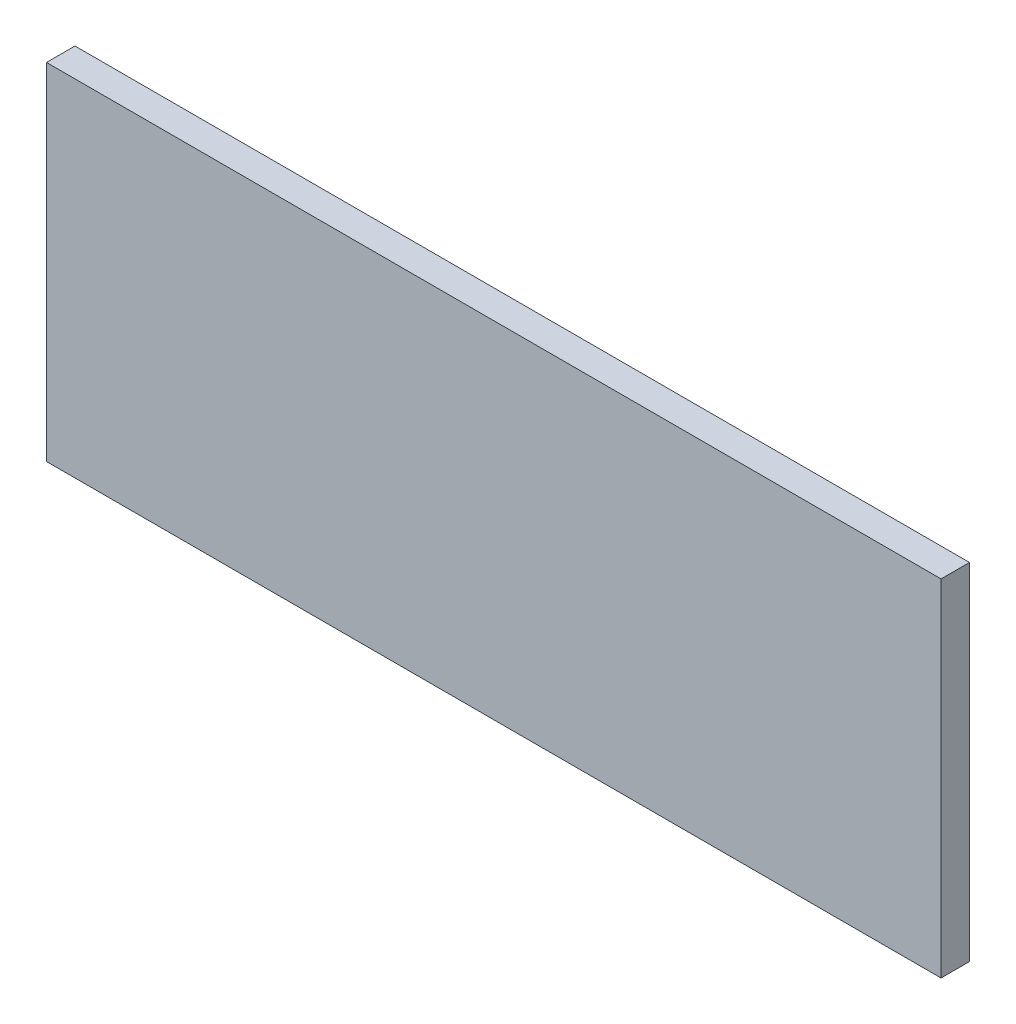
SolidWorks part; units mm, degrees
ref_plane "Ön Düzlem" through (0, 0, 0) normal (0, 0, 1) x (1, 0, 0)
ref_plane "Üst Düzlem" through (0, 0, 0) normal (0, 1, 0) x (1, 0, 0)
ref_plane "Sağ Düzlem" through (0, 0, 0) normal (1, 0, 0) x (0, 0, -1)
sketch "Çizim1" plane through (0, 0, 0) normal (0, 0, 1) x (1, 0, 0)
  line L1 (-44, -17) -> (44, -17)
  line L2 (-44, -17) -> (-44, 17)
  line L3 (-44, 17) -> (44, 17)
  line L4 (44, -17) -> (44, 17)
  line L5 (-44, -17) -> (44, 17) construction
  line L6 (-44, 17) -> (44, -17) construction
  point P0 (0, 0)
extrude "Yükseklik-Ekstrüzyon1" add sketch "Çizim1" along normal blind 2.8
